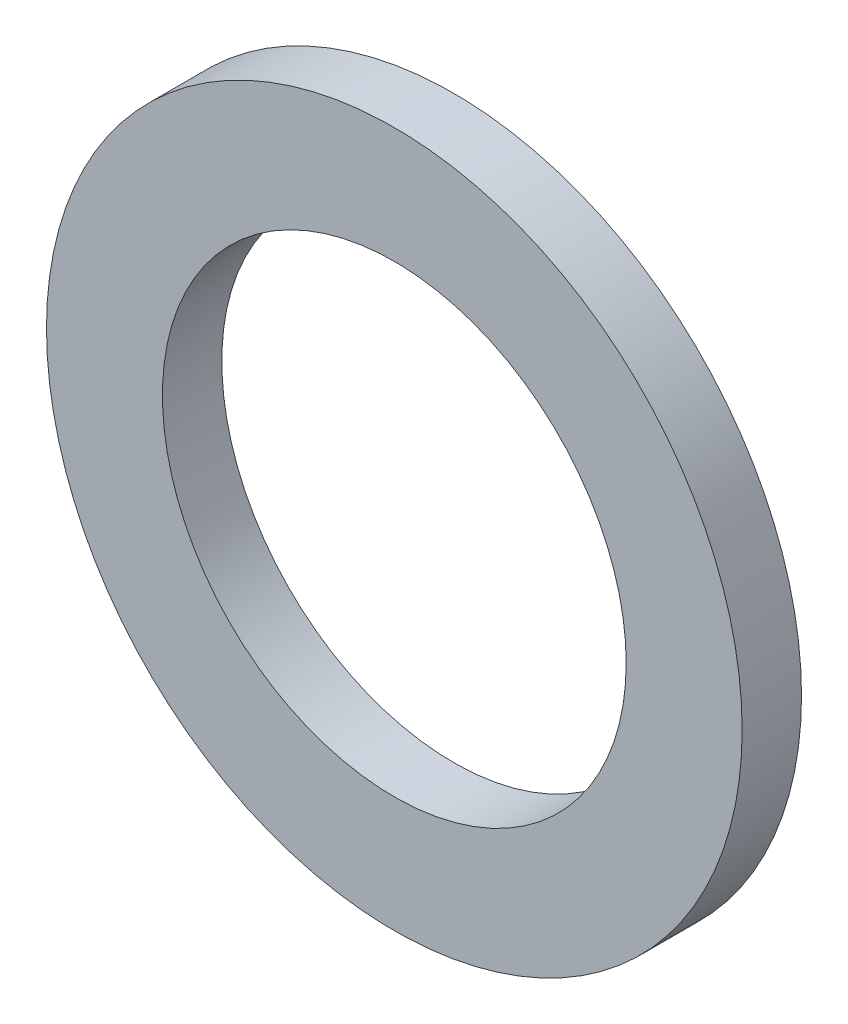
SolidWorks part; units mm, degrees
ref_plane "Front Plane" through (0, 0, 0) normal (0, 0, 1) x (1, 0, 0)
ref_plane "Top Plane" through (0, 0, 0) normal (0, 1, 0) x (1, 0, 0)
ref_plane "Right Plane" through (0, 0, 0) normal (1, 0, 0) x (0, 0, -1)
sketch "Sketch1" plane through (0, 0, 0) normal (0, 0, 1) x (1, 0, 0)
  line L0 (-2.3812, 0) -> (2.3812, 0) construction
  line L1 (0, -2.3812) -> (0, 2.3812) construction
  circle A0 centre (0, 0) radius 2.3812
  circle A1 centre (0, 0) radius 1.5875
  point P4 (0, 0)
  point P9 (0, 0)
  dimension "ID" = 3.175
  dimension "OD" = 4.7625
sketch "Sketch2" plane through (0, 0, 0) normal (1, 0, 0) x (0, 0, -1)
  line L0 (0.2032, 2.3812) -> (-0.2032, 2.3812) construction
  line L1 (0, 2.3812) -> (0, -2.3812) construction
  point P4 (0, 2.3812)
  dimension "Thickness" = 0.4064
sketch "Sketch3" plane through (0, 0, 0) normal (0, 0, 1) x (1, 0, 0)
  line L0 (0, -2.3812) -> (0, 2.3812) construction
  circle A0 centre (0, 0) radius 2.3812
  circle A1 centre (0, 0) radius 1.5875
  circle A2 centre (0, 0) radius 1.5875 construction
extrude "Boss-Extrude1" add sketch "Sketch3" along normal mid plane 0.4064
equation "\"D1@Boss-Extrude1\" = \"Thickness@Sketch2\""
